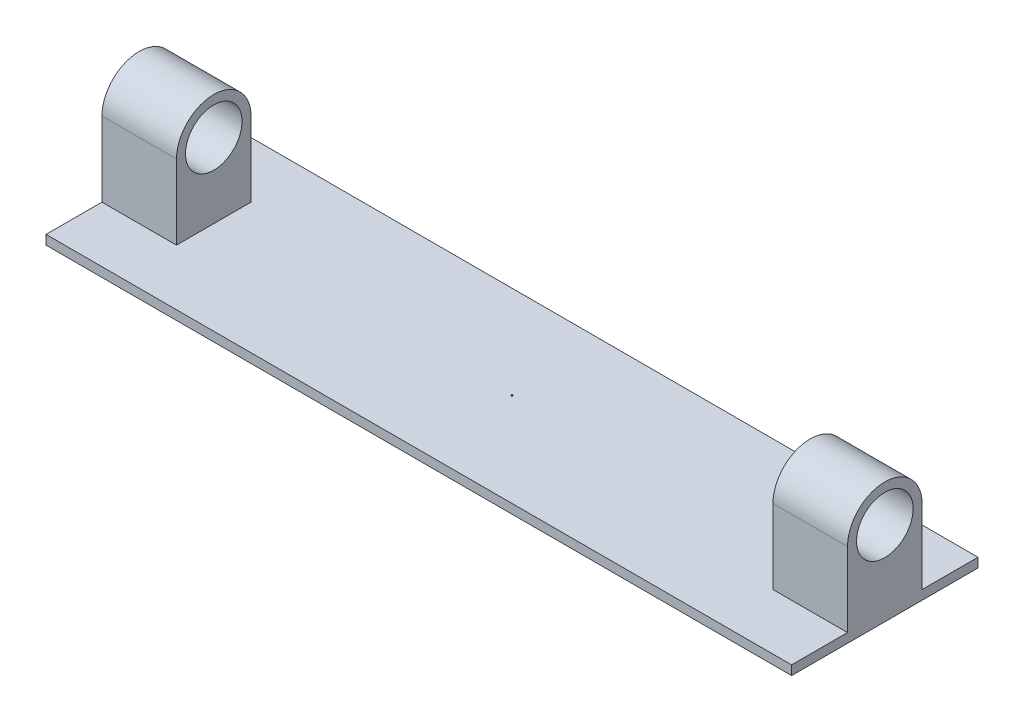
SolidWorks part; units mm, degrees
ref_plane "Front Plane" through (0, 0, 0) normal (0, 0, 1) x (1, 0, 0)
ref_plane "Top Plane" through (0, 0, 0) normal (0, 1, 0) x (1, 0, 0)
ref_plane "Right Plane" through (0, 0, 0) normal (1, 0, 0) x (0, 0, -1)
sketch "Sketch1" plane through (0, 0, 0) normal (0, 1, 0) x (1, 0, 0)
  line L1 (-200, 50) -> (200, 50)
  line L2 (-200, 50) -> (-200, -50)
  line L3 (-200, -50) -> (200, -50)
  line L4 (200, 50) -> (200, -50)
  line L5 (-200, 50) -> (200, -50) construction
  line L6 (-200, -50) -> (200, 50) construction
  point P0 (0, 0)
  dimension "D1" = 400
  dimension "D2" = 100
extrude "Boss-Extrude1" add sketch "Sketch1" along normal blind 5
sketch "Sketch6" plane through (200, 0, 0) normal (1, 0, 0) x (0, 0, -1)
  line L0 (0, 29.8195) -> (0, 34.7063) construction
  line L1 (-50, 5) -> (50, 5) construction
  line L2 (0, 5) -> (0, 25) construction
  line L4 (-20, 45) -> (-20, 5)
  line L5 (-20, 5) -> (20, 5)
  line L6 (20, 45) -> (20, 5)
  line L7 (-3.8503, 64.6259) -> (10.7469, 28.1327) construction
  line L8 (-10.7469, 28.1327) -> (3.8503, 64.6259) construction
  circle A0 centre (0, 45) radius 15.1805
  arc A1 (20, 45) -> (-20, 45) centre (0, 45) ccw
  dimension "D1" = 40
  dimension "D3" = 40
extrude "Boss-Extrude2" add sketch "Sketch6" against normal blind 40
mirror "Mirror1" about plane through (0, 0, 0) normal (1, 0, 0) of "Boss-Extrude2"
sketch "Sketch7" plane through (0, 5, 0) normal (0, 1, 0) x (1, 0, 0)
  line L0 (-200, 50) -> (200, -50) construction
  line L1 (200, 50) -> (-200, -50) construction
  circle A0 centre (0, 0) radius 0.3202
extrude "Boss-Extrude3" add sketch "Sketch7" along normal blind 0.5
